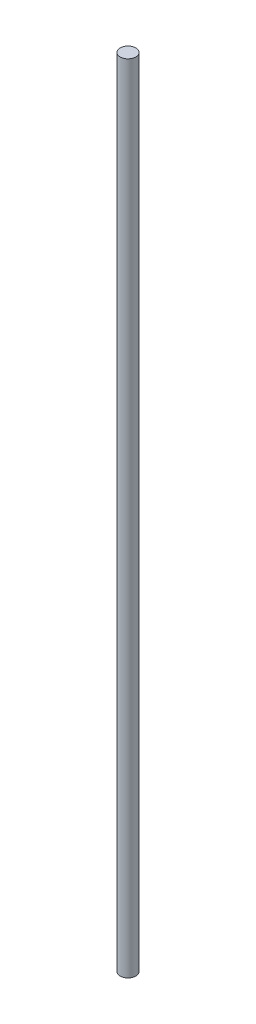
SolidWorks part; units mm, degrees
ref_plane "Front" through (0, 0, 0) normal (0, 0, 1) x (1, 0, 0)
ref_plane "Top" through (0, 0, 0) normal (0, 1, 0) x (1, 0, 0)
ref_plane "Right" through (0, 0, 0) normal (1, 0, 0) x (0, 0, -1)
sketch "Sketch1" plane through (0, 0, 0) normal (0, 1, 0) x (1, 0, 0)
  circle A0 centre (0, 0) radius 4
  dimension "D1" = 8
extrude "Boss-Extrude1" add sketch "Sketch1" along normal blind 405
